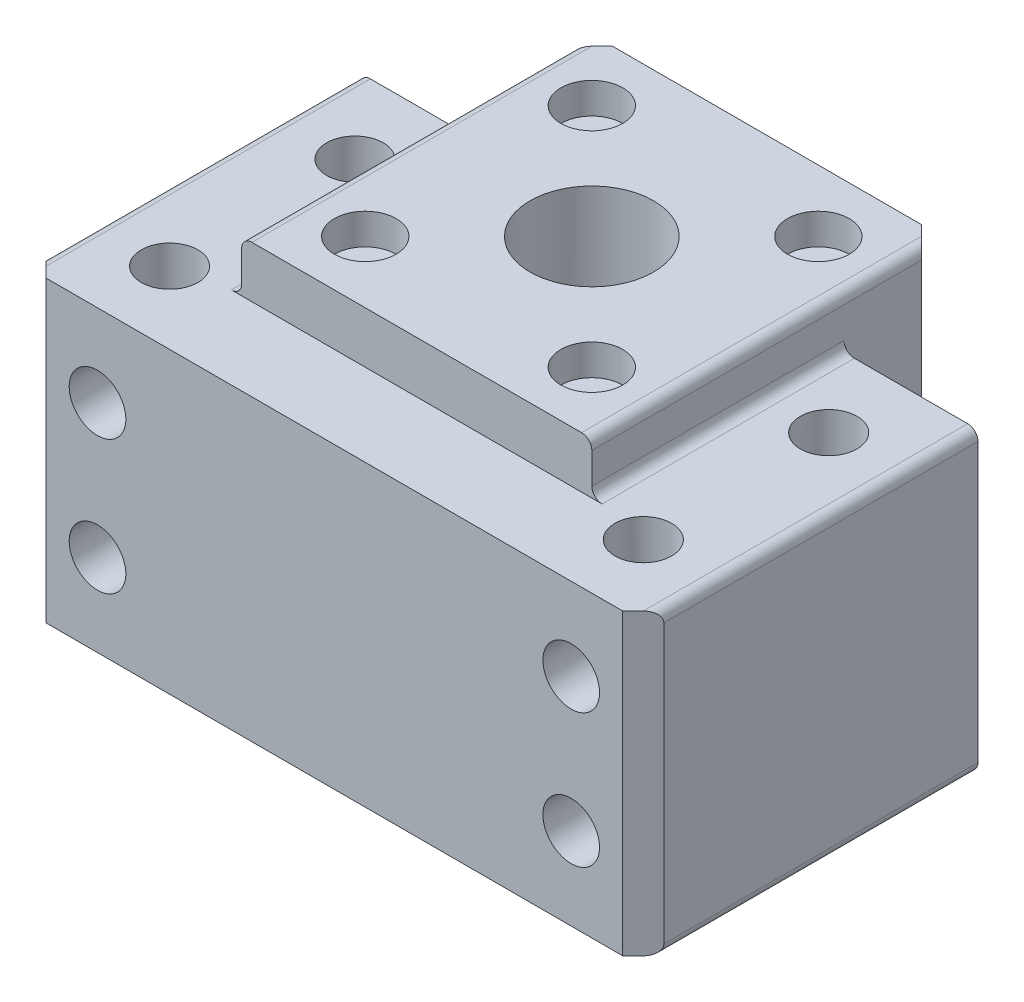
SolidWorks part; units mm, degrees
material "6061 合金"
ref_plane "前视基准面" through (0, 0, 0) normal (0, 0, 1) x (1, 0, 0)
ref_plane "上视基准面" through (0, 0, 0) normal (0, 1, 0) x (1, 0, 0)
ref_plane "右视基准面" through (0, 0, 0) normal (1, 0, 0) x (0, 0, -1)
sketch "草图1" plane through (0, 0, 0) normal (0, 1, 0) x (1, 0, 0)
  line L0 (0, 16.25) -> (0, -16.25) construction
  line L1 (-30, 16.25) -> (30, 16.25)
  line L2 (-30, 16.25) -> (-30, -16.25)
  line L3 (-30, -16.25) -> (30, -16.25)
  line L4 (30, 16.25) -> (30, -16.25)
  line L5 (-30, 16.25) -> (30, -16.25) construction
  line L6 (-30, -16.25) -> (30, 16.25) construction
  line L7 (-23, 16.25) -> (-23, -16.25) construction
  circle A0 centre (0, 8.75) radius 6
  circle A1 centre (-23, 8.75) radius 2.75
  circle A2 centre (-23, -9.25) radius 2.75
  circle A3 centre (23, -9.25) radius 2.75
  circle A4 centre (23, 8.75) radius 2.75
  point P0 (0, 0)
  dimension "D3" = 12
  dimension "D4" = 25
  dimension "D5" = 5.5
  dimension "D6" = 18
  dimension "D7" = 46
  dimension "D1" = 60
  dimension "D2" = 32.5
extrude "凸台-拉伸1" add sketch "草图1" along normal blind 29
sketch "草图2" plane through (0, 0, 0) normal (0, -1, 0) x (1, 0, 0)
  line L1 (17, -25.75) -> (-17, -25.75)
  line L2 (17, -25.75) -> (17, 8.25)
  line L3 (17, 8.25) -> (-17, 8.25)
  line L4 (-17, -25.75) -> (-17, 8.25)
  line L5 (17, -25.75) -> (-17, 8.25) construction
  line L6 (17, 8.25) -> (-17, -25.75) construction
  circle A0 centre (0, -8.75) radius 6 construction
  circle A1 centre (0, -8.75) radius 6
  dimension "D1" = 34
extrude "凸台-拉伸2" add sketch "草图2" against normal blind 34
sketch "草图3" plane through (0, 34, 0) normal (0, 1, 0) x (1, 0, 0)
  line L1 (-11, -2.25) -> (11, -2.25) construction
  line L2 (-11, -2.25) -> (-11, 19.75) construction
  line L3 (-11, 19.75) -> (11, 19.75) construction
  line L4 (11, -2.25) -> (11, 19.75) construction
  line L5 (-11, -2.25) -> (11, 19.75) construction
  line L6 (-11, 19.75) -> (11, -2.25) construction
  circle A0 centre (-11, 19.75) radius 3
  circle A1 centre (11, 19.75) radius 3
  circle A2 centre (-11, -2.25) radius 3
  circle A3 centre (11, -2.25) radius 3
  point P0 (0, 8.75)
  dimension "D1" = 6
  dimension "D2" = 22
extrude "切除-拉伸1" cut sketch "草图3" against normal blind 3
chamfer "倒角1" distance 2 angle 45 4 edges at (-30, 14.5, 16.25) (30, 14.5, 16.25) (-17, 17, -25.75) (17, 17, -25.75)
fillet "圆角1" radius 1 10 edges at (17, 34, -7.75) (-30, 29, -1) (-30, 0, -1) (-17, 0, -20) (-17, 29, -4) (-17, 34, -7.75) (30, 0, -1) (17, 29, -4) (17, 0, -20) (30, 29, -1)
sketch "草图4" plane through (0, 0, -16.25) normal (0, 0, -1) x (-1, 0, 0)
  line L0 (30, 14.5) -> (-30, 14.5) construction
  line L1 (30, 28) -> (30, 1) construction
  line L2 (-30, 28) -> (-30, 1) construction
  line L3 (0, 0) -> (0, 34) construction
  line L4 (15, 0) -> (-15, 0) construction
  line L5 (15, 34) -> (-15, 34) construction
  circle A0 centre (23, 8) radius 3.3
  circle A1 centre (23, 21) radius 3.3
  circle A2 centre (-23, 21) radius 3.3
  circle A3 centre (-23, 8) radius 3.3
  dimension "D1" = 46
  dimension "D2" = 13
  dimension "D3" = 6.6
hole_wizard "M5 六角头螺栓的柱形沉头孔1" positions "3D草图2" profile "草图7" counterbore size "M5" standard "GB" end condition through all
sketch3d "3D草图2"
  point P0 (-23, 8, -16.25)
  point P3 (-23, 21, -16.25)
  point P6 (23, 8, -16.25)
  point P9 (23, 21, -16.25)
sketch "草图7" plane through (-23, 8, -16.25) normal (1, 0, 0) x (0, 1, 0)
  line L0 (0, 0) -> (0, 32.5)
  line L1 (0, 32.5) -> (2.75, 32.5)
  line L3 (2.75, 32.5) -> (2.75, 0.5)
  line L4 (5.5, 0.5) -> (2.75, 0.5)
  line L5 (5.5, 0.5) -> (5.5, 0.025)
  line L6 (5.5, 0.025) -> (5.525, 0)
  line L7 (5.525, 0) -> (0, 0)
  line L8 (-5.5, 0.025) -> (-5.525, 0) construction
  line L11 (0, -6.35) -> (0, 107.95) construction
  dimension "通孔孔直径" = 5.5
  dimension "通孔孔深度" = 32.5
  dimension "柱形沉头孔直径" = 11
  dimension "柱形沉头孔深度" = 0.5
  dimension "近端锥形沉头孔直径" = 11.05
  dimension "近端锥形沉头孔角度" = 90
